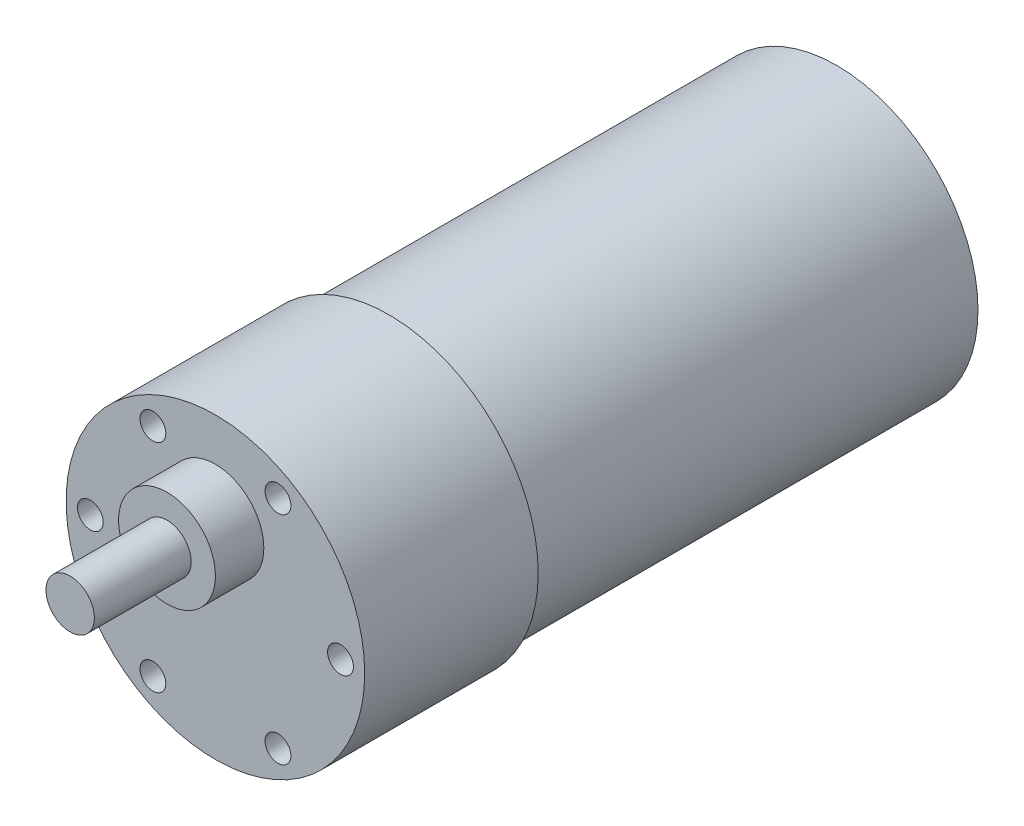
SolidWorks part; units mm, degrees
ref_plane "Plano frontal" through (0, 0, 0) normal (0, 0, 1) x (1, 0, 0)
ref_plane "Plano superior" through (0, 0, 0) normal (0, 1, 0) x (1, 0, 0)
ref_plane "Plano direito" through (0, 0, 0) normal (1, 0, 0) x (0, 0, -1)
sketch "Esboço1" plane through (0, 0, 0) normal (0, 0, 1) x (1, 0, 0)
  circle A0 centre (0, 0) radius 18.5
  dimension "D1" = 37
extrude "Ressalto-extrusão1" add sketch "Esboço1" against normal blind 21.5 contours A0
sketch "Esboço2" plane through (0, 0, -21.5) normal (0, 0, -1) x (-1, 0, 0)
  circle A0 centre (0, 0) radius 17.5
  dimension "D1" = 35
extrude "Ressalto-extrusão2" add sketch "Esboço2" along normal blind 55.5
sketch "Esboço5" plane through (0, 0, 0) normal (0, 0, 1) x (1, 0, 0)
  line L0 (0, 18.5) -> (0, -18.5) construction
  circle A0 centre (0, 0) radius 18.5 construction
  circle A1 centre (0, 7.2) radius 6
  dimension "D1" = 12
  dimension "D2" = 11.3
extrude "Ressalto-extrusão6" add sketch "Esboço5" along normal blind 6
sketch "Esboço6" plane through (0, 0, 6) normal (0, 0, 1) x (1, 0, 0)
  circle A0 centre (0, 7.2) radius 3
  dimension "D1" = 6
extrude "Ressalto-extrusão7" add sketch "Esboço6" along normal blind 12
sketch "Esboço7" plane through (0, 0, 0) normal (0, 0, 1) x (1, 0, 0)
  line L0 (0, 0) -> (0, 15.5) construction
  line L1 (0, 0) -> (-7.75, 13.4234) construction
  circle A0 centre (0, 0) radius 15.5
  circle A1 centre (-7.75, 13.4234) radius 1.6
  circle A2 centre (7.75, 13.4234) radius 1.6
  circle A3 centre (15.5, 0) radius 1.6
  circle A4 centre (7.75, -13.4234) radius 1.6
  circle A5 centre (-7.75, -13.4234) radius 1.6
  circle A6 centre (-15.5, 0) radius 1.6
  point P3 (0, 0)
  point P19 (0, 0)
  dimension "D1" = 31
  dimension "D3" = 3.2
  dimension "D2" = 30
  dimension "D4" = 6
extrude "Corte-extrusão1" cut sketch "Esboço7" against normal blind 6 contours A0 A6 | A0 A6 | A0 A1 | A0 A1 | A0 A2 | A0 A2 | A0 A3 | A0 A3 | A0 A4 | A0 A4 | A0 A5 | A0 A5
